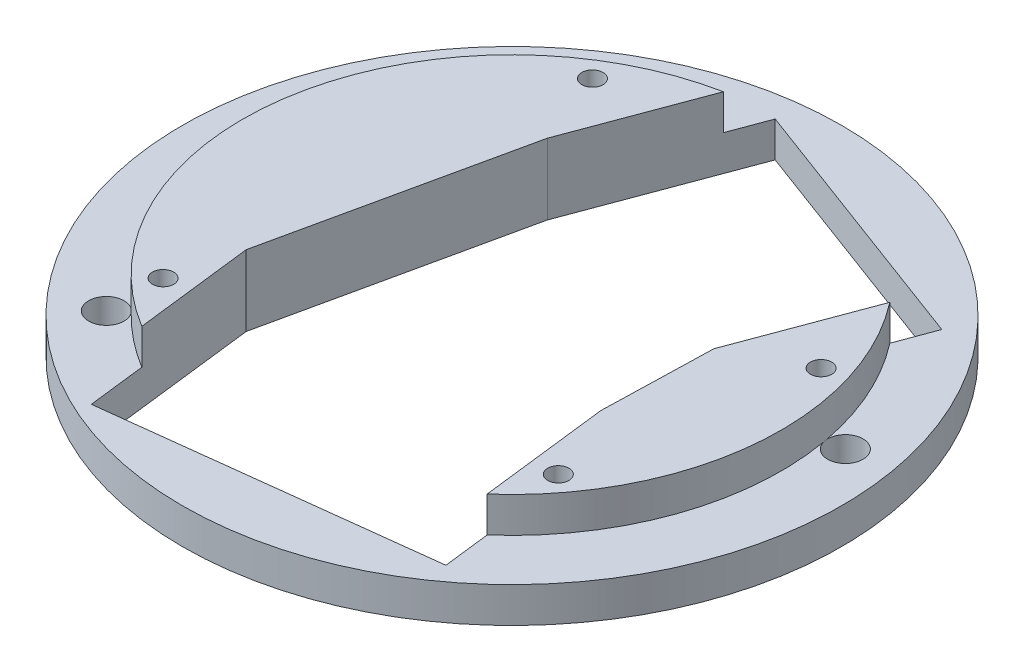
SolidWorks part; units mm, degrees
ref_plane "Plan de face" through (0, 0, 0) normal (0, 0, 1) x (1, 0, 0)
ref_plane "Plan de dessus" through (0, 0, 0) normal (0, 1, 0) x (1, 0, 0)
ref_plane "Plan de droite" through (0, 0, 0) normal (1, 0, 0) x (0, 0, -1)
sketch "Esquisse1" plane through (0, 0, 0) normal (0, 1, 0) x (1, 0, 0)
  circle A0 centre (-2.8352, 0) radius 46.5
extrude "Boss.-Extru.1" add sketch "Esquisse1" along normal blind 5
sketch "Esquisse3" plane through (0, 5, 0) normal (0, 1, 0) x (1, 0, 0)
  circle A0 centre (-2.8352, 0) radius 38
  circle A1 centre (-2.8352, 0) radius 46.5 construction
  dimension "D1" = 0
extrude "Boss.-Extru.2" add sketch "Esquisse3" along normal blind 5
sketch "Esquisse4" plane through (0, 5, 0) normal (0, 1, 0) x (1, 0, 0)
  circle A0 centre (-2.8352, 0) radius 40.4798
  circle A1 centre (-2.8352, 0) radius 46.5 construction
  circle A2 centre (-21.2489, 36.0493) radius 2.5
  circle A3 centre (36.9989, 7.2013) radius 2.5
  circle A4 centre (-32.0188, -28.0523) radius 2.5
  dimension "D1" = 0
  dimension "D2" = 65
  dimension "D3" = 65
  dimension "D4" = 77.5
extrude "Enlèv. mat.-Extru.1" cut sketch "Esquisse4" against normal through all contours A2 | A3 | A4
sketch "Esquisse5" plane through (0, 10, 0) normal (0, 1, 0) x (1, 0, 0)
  circle A0 centre (-2.8352, 0) radius 34.8185
  circle A1 centre (-2.8352, 0) radius 38 construction
  circle A2 centre (-27.0188, -25.0496) radius 1.5
  circle A3 centre (24.8338, -21.1365) radius 1.5
  circle A4 centre (30.4015, 10.3754) radius 1.5
  circle A5 centre (-21.1169, 29.6328) radius 1.5
  arc A6 (-30.4432, -26.1112) -> (-30.017, -26.5547) centre (-32.0188, -28.0523) ccw construction
  dimension "D1" = 0
  dimension "D2" = 55
  dimension "D6" = 5
  dimension "D3" = 32
  dimension "D4" = 52
  dimension "D5" = 55
extrude "Enlèv. mat.-Extru.2" cut sketch "Esquisse5" against normal through all contours A2 | A5 | A4 | A3
sketch "Esquisse6" plane through (0, 10, 0) normal (0, 1, 0) x (1, 0, 0)
  line L0 (-17.0166, 19.1586) -> (-8.2861, 42.5846)
  line L1 (-8.2861, 42.5846) -> (29.1955, 28.6159)
  line L2 (29.1955, 28.6159) -> (20.465, 5.1899)
  line L3 (20.465, 5.1899) -> (-17.0166, 19.1586)
  circle A0 centre (30.4015, 10.3754) radius 1.5 construction
  circle A1 centre (-21.1169, 29.6328) radius 1.5 construction
  circle A2 centre (-2.8352, 0) radius 38 construction
  dimension "D1" = 7.5
  dimension "D2" = 7.5
  dimension "D3" = 38
  dimension "D4" = 25
extrude "Enlèv. mat.-Extru.4" cut sketch "Esquisse6" against normal through all
sketch "Esquisse7" plane through (0, 10, 0) normal (0, 1, 0) x (1, 0, 0)
  line L0 (-24.6381, -15.7037) -> (-21.6657, -40.5263)
  line L1 (-21.6657, -40.5263) -> (23.0151, -35.176)
  line L2 (23.0151, -35.176) -> (20.0427, -10.3533)
  line L3 (20.0427, -10.3533) -> (-24.6381, -15.7037)
  circle A0 centre (-27.0188, -25.0496) radius 1.5 construction
  circle A1 centre (24.8338, -21.1365) radius 1.5 construction
  arc A2 (-30.017, -26.5547) -> (34.6121, 6.4573) centre (-2.8352, 0) ccw construction
  point P6 (-23.1519, -28.115)
  dimension "D5" = 38
  dimension "D1" = 3.475
  dimension "D2" = 45
  dimension "D3" = 25
  dimension "D4" = 3.475
extrude "Enlèv. mat.-Extru.5" cut sketch "Esquisse7" against normal through all
sketch "Esquisse8" plane through (0, 10, 0) normal (0, 1, 0) x (1, 0, 0)
  line L0 (-17.0166, 19.1586) -> (-24.6381, -15.7037)
  line L1 (20.465, 5.1899) -> (20.0427, -10.3533)
  line L2 (-24.6381, -15.7037) -> (20.0427, -10.3533)
  line L3 (-17.0166, 19.1586) -> (20.465, 5.1899)
extrude "Enlèv. mat.-Extru.6" cut sketch "Esquisse8" against normal through all
